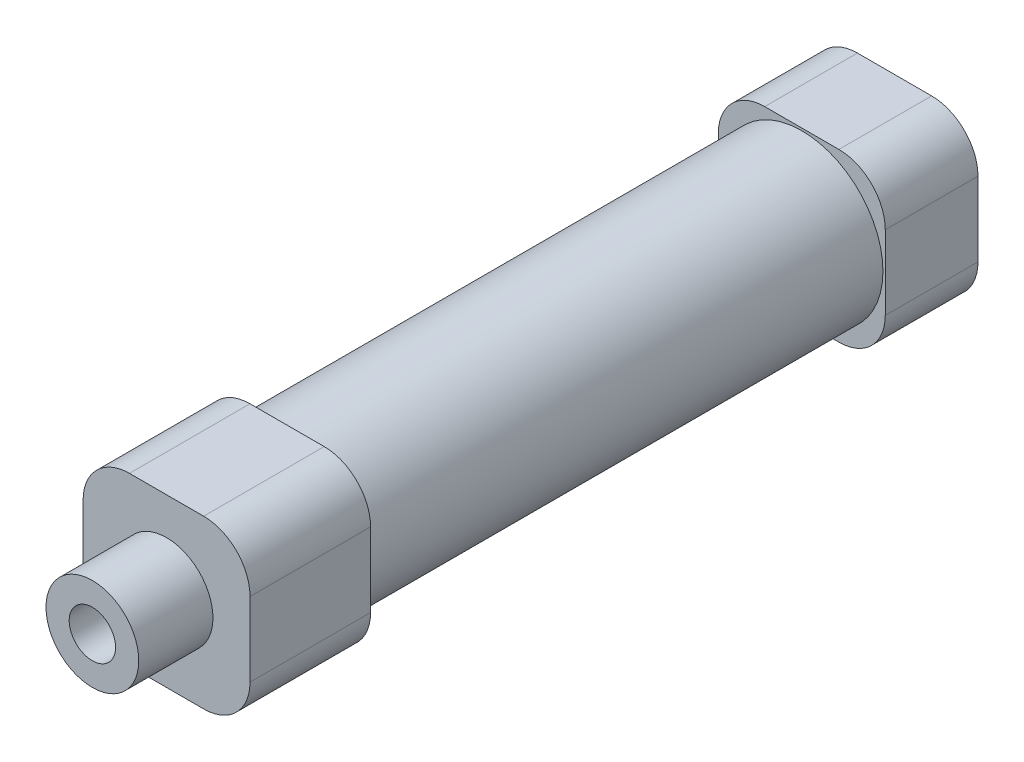
SolidWorks part; units mm, degrees
ref_plane "前视基准面" through (0, 0, 0) normal (0, 0, 1) x (1, 0, 0)
ref_plane "上视基准面" through (0, 0, 0) normal (0, 1, 0) x (1, 0, 0)
ref_plane "右视基准面" through (0, 0, 0) normal (1, 0, 0) x (0, 0, -1)
sketch "草图1" plane through (0, 0, 0) normal (0, 0, 1) x (1, 0, 0)
  line L1 (-9, 9) -> (9, 9)
  line L2 (-9, 9) -> (-9, -9)
  line L3 (-9, -9) -> (9, -9)
  line L4 (9, 9) -> (9, -9)
  line L5 (-9, 9) -> (9, -9) construction
  line L6 (-9, -9) -> (9, 9) construction
  point P0 (0, 0)
  dimension "D1" = 18
  dimension "D2" = 18
extrude "凸台-拉伸1" add sketch "草图1" along normal blind 10
sketch "草图2" plane through (0, 0, 10) normal (0, 0, 1) x (1, 0, 0)
  line L0 (0, 9) -> (0, -9) construction
  line L1 (9, 9) -> (-9, 9) construction
  line L2 (-9, -9) -> (9, -9) construction
  circle A0 centre (0, 0) radius 8.75
  dimension "D1" = 17.5
extrude "凸台-拉伸2" add sketch "草图2" along normal blind 55.5
sketch "草图3" plane through (0, 0, 65.5) normal (0, 0, 1) x (1, 0, 0)
  line L1 (-9, -9) -> (9, -9)
  line L2 (-9, -9) -> (-9, 9)
  line L3 (-9, 9) -> (9, 9)
  line L4 (9, -9) -> (9, 9)
  line L5 (-9, -9) -> (9, 9) construction
  line L6 (-9, 9) -> (9, -9) construction
  point P0 (0, 0)
extrude "凸台-拉伸3" add sketch "草图3" along normal blind 13
sketch "草图4" plane through (0, 0, 78.5) normal (0, 0, 1) x (1, 0, 0)
  circle A0 centre (0, 0) radius 5
  dimension "D1" = 10
extrude "凸台-拉伸4" add sketch "草图4" along normal blind 8
cosmetic thread "装饰螺纹线1" parameters "D2"=6.941
sketch "草图5" plane through (0, 0, 86.5) normal (0, 0, 1) x (1, 0, 0)
  circle A0 centre (0, 0) radius 2.5
  dimension "D1" = 5
extrude "切除-拉伸1" cut sketch "草图5" against normal offset from surface (85.5 mm away) 1 up to face at (0, 0, 0)
fillet "圆角1" radius 5 8 edges at (-9, 9, 72) (-9, -9, 72) (9, -9, 5) (9, -9, 72) (9, 9, 5) (9, 9, 72) (-9, 9, 5) (-9, -9, 5)
sketch "草图6" plane through (0, -9, 0) normal (0, -1, 0) x (1, 0, 0)
  line L0 (4, 5.25) -> (-4, 5.25) construction
  line L1 (4, 0) -> (4, 10) construction
  line L2 (-4, 10) -> (-4, 0) construction
  line L3 (-4, 10) -> (4, 10) construction
  line L4 (4, 70.25) -> (-4, 70.25) construction
  line L5 (4, 65.5) -> (4, 78.5) construction
  line L6 (-4, 78.5) -> (-4, 65.5) construction
  line L8 (-4, 65.5) -> (4, 65.5) construction
  circle A0 centre (0, 5.25) radius 2.5
  circle A1 centre (0, 70.25) radius 2.5
  dimension "D2" = 5
  dimension "D4" = 5
  dimension "D1" = 4.75
  dimension "D3" = 4.75
extrude "切除-拉伸2" cut sketch "草图6" against normal up to surface (9 mm away) up to plane "上视基准面"
